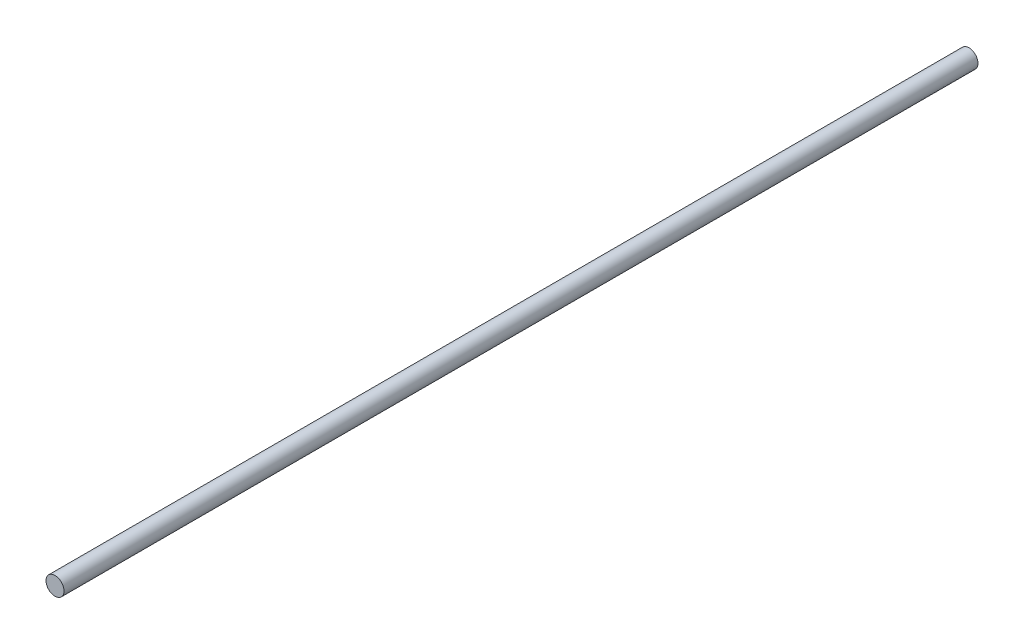
SolidWorks part; units mm, degrees
ref_plane "Front Plane" through (0, 0, 0) normal (0, 0, 1) x (1, 0, 0)
ref_plane "Top Plane" through (0, 0, 0) normal (0, 1, 0) x (1, 0, 0)
ref_plane "Right Plane" through (0, 0, 0) normal (1, 0, 0) x (0, 0, -1)
sketch "Sketch1" plane through (0, 0, 0) normal (0, 0, 1) x (1, 0, 0)
  circle A0 centre (0, 0) radius 2.3813
  dimension "D1" = 4.7625
extrude "Boss-Extrude1" add sketch "Sketch1" along normal blind 241.3
